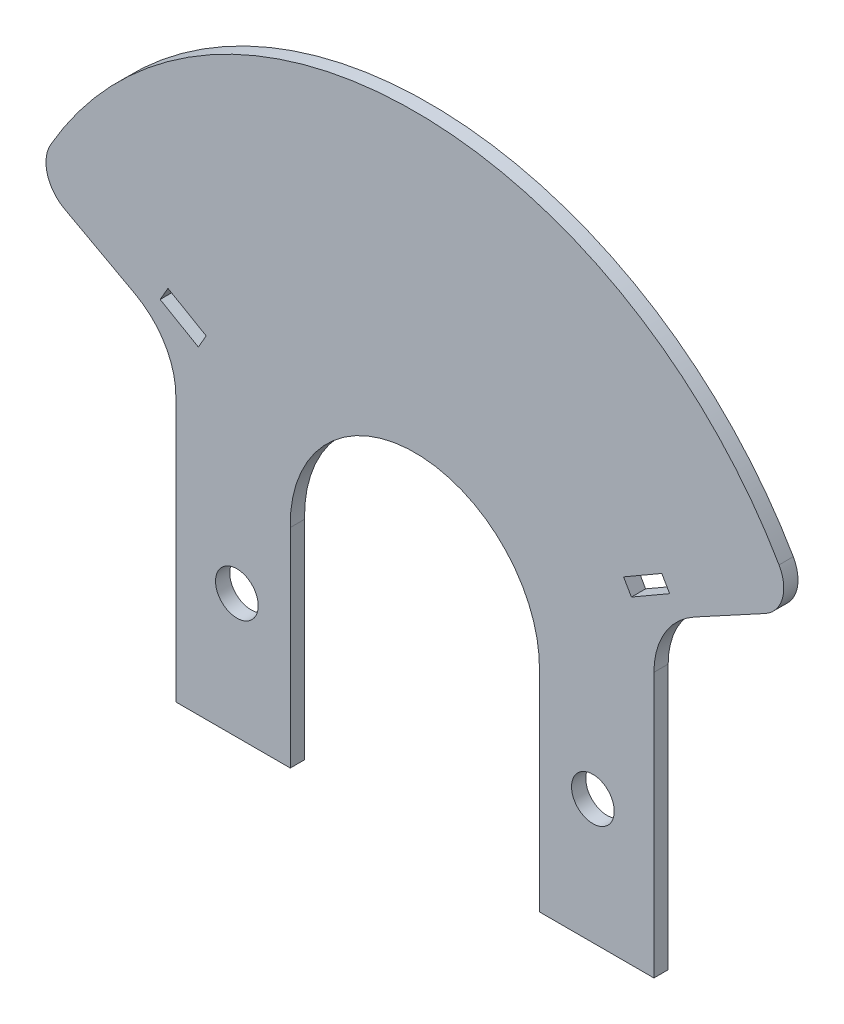
SolidWorks part; units mm, degrees
ref_plane "Front Plane" through (0, 0, 0) normal (0, 0, 1) x (1, 0, 0)
ref_plane "Top Plane" through (0, 0, 0) normal (0, 1, 0) x (1, 0, 0)
ref_plane "Right Plane" through (0, 0, 0) normal (1, 0, 0) x (0, 0, -1)
sketch "Sketch1" plane through (0, 0, 0) normal (0, 0, 1) x (1, 0, 0)
  line L93 (35.5802, 19.684) -> (36.6302, 17.8654) construction
  line L94 (30.2974, 16.634) -> (35.5802, 19.684) construction
  line L95 (31.3474, 14.8154) -> (30.2974, 16.634) construction
  line L100 (36.6302, 17.8654) -> (31.3474, 14.8154) construction
  line L102 (-36.6302, 17.8654) -> (-31.3474, 14.8154) construction
  line L103 (-35.5802, 19.684) -> (-36.6302, 17.8654) construction
  line L104 (-30.2974, 16.634) -> (-35.5802, 19.684) construction
  line L105 (-31.3474, 14.8154) -> (-30.2974, 16.634) construction
  line L108 (-17.5, -29.9861) -> (-33.5704, -29.9861)
  line L109 (-33.5704, -29.9861) -> (-33.5704, 7.1917)
  line L110 (33.5704, -29.9861) -> (33.5704, 7.1917)
  line L111 (17.5, -29.9861) -> (33.5704, -29.9861)
  line L114 (-39.2683, 16.7677) -> (-53.5006, 24.4929)
  line L115 (39.2683, 16.7677) -> (53.5006, 24.4929)
  line L117 (-17.5, -0.732) -> (-17.5, -29.9861)
  line L118 (17.5, -0.732) -> (17.5, -29.9861)
  line L123 (-35.7776, 17.8654) -> (-30.4083, 14.7654)
  line L124 (-30.4083, 14.7654) -> (-29.3083, 16.6706)
  line L125 (-29.3083, 16.6706) -> (-34.6776, 19.7706)
  line L126 (-34.6776, 19.7706) -> (-35.7776, 17.8654)
  line L127 (-35.641, 17.902) -> (-30.4449, 14.902) construction
  line L128 (-34.641, 19.634) -> (-35.641, 17.902) construction
  line L129 (-29.4449, 16.634) -> (-34.641, 19.634) construction
  line L130 (-30.4449, 14.902) -> (-29.4449, 16.634) construction
  line L131 (30.4449, 14.902) -> (29.4449, 16.634) construction
  line L132 (35.641, 17.902) -> (30.4449, 14.902) construction
  line L133 (34.641, 19.634) -> (35.641, 17.902) construction
  line L134 (29.4449, 16.634) -> (34.641, 19.634) construction
  line L135 (30.4083, 14.7654) -> (29.3083, 16.6706)
  line L136 (29.3083, 16.6706) -> (34.6776, 19.7706)
  line L137 (34.6776, 19.7706) -> (35.7776, 17.8654)
  line L138 (35.7776, 17.8654) -> (30.4083, 14.7654)
  circle A7 centre (-25, -12.5) radius 3
  circle A8 centre (25, -12.5) radius 3
  arc A15 (53.5006, 24.4929) -> (-53.5006, 24.4929) centre (0, -0.366) ccw
  arc A19 (33.5704, 7.1917) -> (39.2683, 16.7677) centre (44.4661, 7.1917) cw
  arc A20 (-33.5704, 7.1917) -> (-39.2683, 16.7677) centre (-44.4661, 7.1917) ccw
  arc A24 (17.5, -0.732) -> (-17.5, -0.732) centre (0, -0.366) ccw
  point P3 (-32.0584, 19.684)
  point P6 (33.5704, 13.6749)
  point P15 (0, 0)
  point P34 (-33.5704, 13.6749)
  point P38 (16.5704, 4.3949)
  point P41 (-16.5704, 4.3949)
  dimension "D1" = 10.8958
  dimension "D4" = 6
  dimension "D2" = 0.1
  dimension "D6" = 2.1
  dimension "D3" = 0.1
  dimension "D5" = 50
  dimension "D7" = 6.1
extrude "Boss-Extrude1" add sketch "Sketch1" along normal blind 2
fillet "Fillet1" radius 5 2 edges at (-53.5006, 24.4929, 1) (53.5006, 24.4929, 1)
